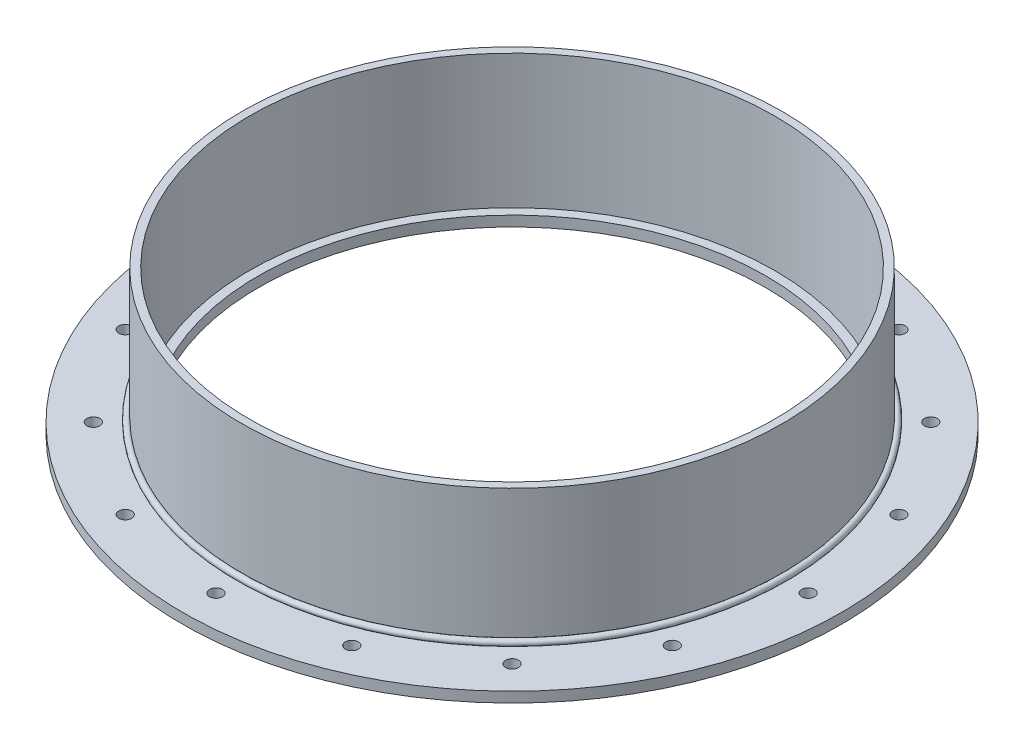
SolidWorks part; units mm, degrees
ref_plane "Front" through (0, 0, 0) normal (0, 0, 1) x (1, 0, 0)
ref_plane "Top" through (0, 0, 0) normal (0, 1, 0) x (1, 0, 0)
ref_plane "Right" through (0, 0, 0) normal (1, 0, 0) x (0, 0, -1)
sketch "Sketch1" plane through (0, 0, 0) normal (0, 0, 1) x (1, 0, 0)
  line L0 (0, 0) -> (0, 26.292) construction
  line L1 (-156.3688, 0) -> (-203.2, 0)
  line L2 (-156.3688, 0) -> (-156.3688, 6.35)
  line L3 (-156.3688, 6.35) -> (-203.2, 6.35)
  line L4 (-203.2, 0) -> (-203.2, 6.35)
  dimension "D1" = 6.35
  dimension "D2" = 406.4
  dimension "D3" = 312.7375
revolve "Revolve1" add sketch "Sketch1" angle 360 about L0
sketch "Sketch2" plane through (0, 0, 0) normal (0, 0, 1) x (1, 0, 0)
  line L0 (203.2, 6.35) -> (-203.2, 6.35) construction
  line L1 (-166.6875, 6.35) -> (-161.925, 6.35)
  line L2 (-166.6875, 6.35) -> (-166.6875, 88.9)
  line L3 (-166.6875, 88.9) -> (-161.925, 88.9)
  line L4 (-161.925, 6.35) -> (-161.925, 88.9)
  line L5 (0, 0) -> (0, 56.4767) construction
  line L6 (-203.2, 0) -> (203.2, 0) construction
  dimension "D1" = 4.7625
  dimension "D2" = 323.85
  dimension "D3" = 88.9
revolve "Revolve2" add sketch "Sketch2" angle 360 about L5
sketch "Sketch3" plane through (0, 0, 0) normal (0, 0, 1) x (1, 0, 0)
  line L0 (-167.9109, 7.5734) -> (-166.6875, 6.35) construction
  line L1 (203.2, 6.35) -> (-203.2, 6.35) construction
  line L2 (-166.6875, 6.35) -> (-169.4733, 6.35)
  line L3 (-166.6875, 88.9) -> (-166.6875, 6.35) construction
  line L4 (-166.6875, 9.1358) -> (-166.6875, 6.35)
  line L5 (0, 0) -> (0, 19.0297) construction
  arc A0 (-166.6875, 9.1358) -> (-169.4733, 6.35) centre (-167.9109, 7.5734) ccw
  dimension "D1" = 3.9688
  dimension "D2" = 45
  dimension "D3" = 2.7858
revolve "Revolve3" add sketch "Sketch3" angle 360 about L5
sketch "Sketch4" plane through (0, 6.35, 0) normal (0, 1, 0) x (1, 0, 0)
  circle A0 centre (0, 182.5625) radius 3.9687
  circle A1 centre (0, 0) radius 182.5625 construction
  dimension "D1" = 365.125
  dimension "D2" = 7.9375
extrude "Cut-Extrude1" cut sketch "Sketch4" against normal through all
pattern_circular "CirPattern1" count 16 over 360 about axis through (0, 0, 0) along (0, 1, 0) of "Cut-Extrude1"
